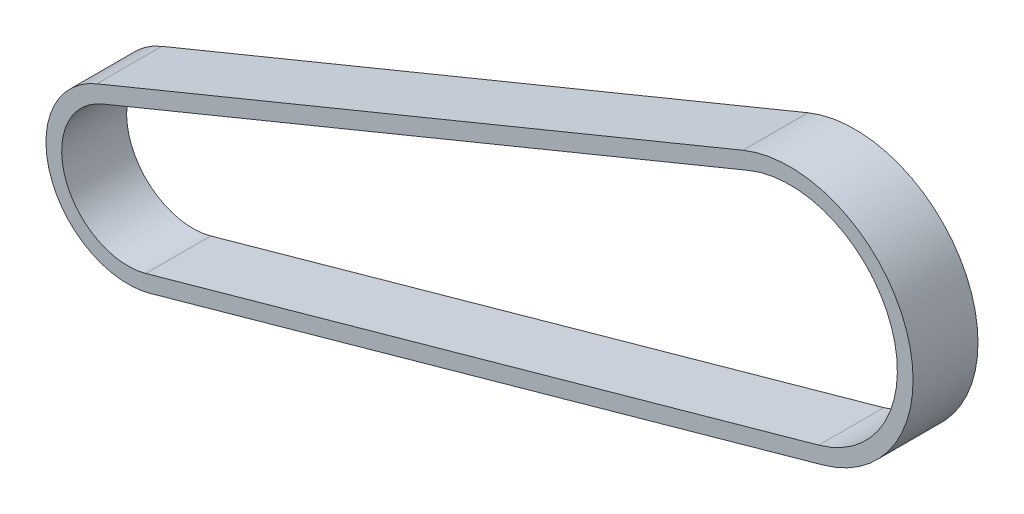
SolidWorks part; units mm, degrees
material "NEOPRENE"
ref_plane "Front Plane" through (0, 0, 0) normal (0, 0, 1) x (1, 0, 0)
ref_plane "Top Plane" through (0, 0, 0) normal (0, 1, 0) x (1, 0, 0)
ref_plane "Right Plane" through (0, 0, 0) normal (1, 0, 0) x (0, 0, -1)
sketch "Sketch2" plane through (0, 0, 0) normal (0, 0, 1) x (1, 0, 0)
  line L0 (0, 0) -> (1, 0) construction
  line L1 (0, 0) -> (0, 1) construction
  line L2 (2.67, -9.5671) -> (-59.5029, -26.9186)
  line L3 (-63.4792, -15.3491) -> (-3.7756, 9.1871)
  arc A0 (-3.7756, 9.1871) -> (2.67, -9.5671) centre (0, 0) cw
  arc A1 (-59.5029, -26.9186) -> (-63.4792, -15.3491) centre (-61.15, -21.0167) cw
ref_plane "Plane1" through (-63.4792, -15.3491, 0) normal (0.9249, 0.3801, 0) x (0, 0, -1)
sketch "Sketch3" plane through (-63.4792, -15.3491, 0) normal (0.9249, 0.3801, 0) x (0, 0, -1)
  line L0 (3, 1.45) -> (3, 0)
  line L1 (3, 1.45) -> (-3, 1.45)
  line L2 (3, 0) -> (-3, 0)
  line L3 (-3, 1.45) -> (-3, 0)
  line L4 (3, 1.45) -> (-3, 0) construction
  line L5 (3, 0) -> (-3, 1.45) construction
  point P0 (0, 0)
  point P1 (0, 0.725)
  dimension "D1" = 1.45
  dimension "D2" = 6
sweep "Sweep1" add profiles "Sketch3" path "Sketch2"
